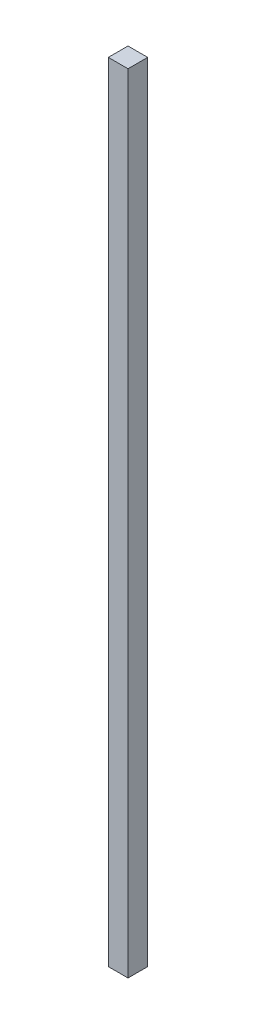
SolidWorks part; units mm, degrees
ref_plane "Front Plane" through (0, 0, 0) normal (0, 0, 1) x (1, 0, 0)
ref_plane "Top Plane" through (0, 0, 0) normal (0, 1, 0) x (1, 0, 0)
ref_plane "Right Plane" through (0, 0, 0) normal (1, 0, 0) x (0, 0, -1)
sketch "Sketch1" plane through (0, 0, 0) normal (0, 1, 0) x (1, 0, 0)
  line L1 (-1, 1) -> (1, 1)
  line L2 (-1, 1) -> (-1, -1)
  line L3 (-1, -1) -> (1, -1)
  line L4 (1, 1) -> (1, -1)
  line L5 (-1, 1) -> (1, -1) construction
  line L6 (-1, -1) -> (1, 1) construction
  point P0 (0, 0)
  dimension "D1" = 2
  dimension "D2" = 2
extrude "Boss-Extrude1" add sketch "Sketch1" along normal blind 80
